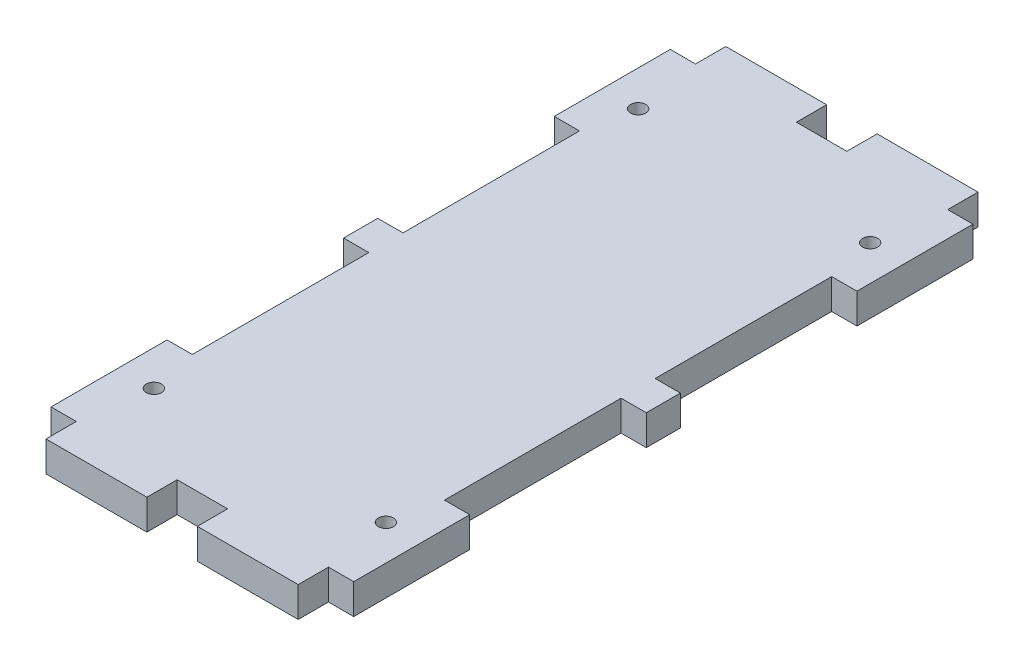
SolidWorks part; units mm, degrees
ref_plane "Plan de face" through (0, 0, 0) normal (0, 0, 1) x (1, 0, 0)
ref_plane "Plan de dessus" through (0, 0, 0) normal (0, 1, 0) x (1, 0, 0)
ref_plane "Plan de droite" through (0, 0, 0) normal (1, 0, 0) x (0, 0, -1)
sketch "Esquisse1" plane through (0, 0, 0) normal (0, 1, 0) x (1, 0, 0)
  line L0 (0, 89.2093) -> (0, -94.1785) construction
  line L1 (-30, 61.38) -> (30, 61.38)
  line L2 (-30, 61.38) -> (-30, -61.38)
  line L3 (-30, -61.38) -> (30, -61.38)
  line L4 (30, 61.38) -> (30, -61.38)
  dimension "D1" = 60
  dimension "D2" = 122.76
  dimension "D3" = 61.38
  dimension "D4" = 30
extrude "Boss.-Extru.1" add sketch "Esquisse1" along normal blind 6
sketch "Esquisse2" plane through (0, 6, 0) normal (0, 1, 0) x (1, 0, 0)
  line L0 (30, 61.38) -> (-30, 61.38) construction
  line L1 (-25, 61.38) -> (-5, 61.38)
  line L2 (-25, 61.38) -> (-25, 67.38)
  line L3 (-25, 67.38) -> (-5, 67.38)
  line L4 (-5, 61.38) -> (-5, 67.38)
  line L6 (5, 61.38) -> (25, 61.38)
  line L7 (5, 61.38) -> (5, 67.38)
  line L8 (5, 67.38) -> (25, 67.38)
  line L9 (25, 61.38) -> (25, 67.38)
  line L10 (-30, 61.38) -> (-30, -61.38) construction
  line L11 (30, -61.38) -> (30, 61.38) construction
  line L12 (-114.0924, 0) -> (165.6917, 0) construction
  line L13 (25, -61.38) -> (25, -67.38)
  line L14 (5, -67.38) -> (25, -67.38)
  line L15 (5, -61.38) -> (5, -67.38)
  line L16 (5, -61.38) -> (25, -61.38)
  line L17 (-5, -61.38) -> (-5, -67.38)
  line L18 (-25, -67.38) -> (-5, -67.38)
  line L19 (-25, -61.38) -> (-25, -67.38)
  line L20 (-25, -61.38) -> (-5, -61.38)
  dimension "D1" = 6
  dimension "D2" = 20
  dimension "D3" = 6
  dimension "D4" = 20
  dimension "D5" = 5
  dimension "D6" = 5
extrude "Boss.-Extru.2" add sketch "Esquisse2" against normal blind 6
sketch "Esquisse3" plane through (0, 6, 0) normal (0, 1, 0) x (1, 0, 0)
  line L0 (73.2715, 0) -> (-73.7315, 0) construction
  line L1 (-60.2107, 48) -> (82.7649, 48) construction
  line L2 (-25, 61.38) -> (-30, 61.38) construction
  line L3 (30, -61.38) -> (30, 61.38) construction
  circle A0 centre (23, 48) radius 1.5
  circle A1 centre (-23, 48) radius 1.5
  circle A2 centre (-23, -48) radius 1.5
  circle A3 centre (23, -48) radius 1.5
  point P5 (-27.5, 61.38)
  dimension "D3" = 3
  dimension "D4" = 3
  dimension "D5" = 46
  dimension "D1" = 13.38
  dimension "D2" = 7
extrude "Enlèv. mat.-Extru.1" cut sketch "Esquisse3" against normal blind 6
sketch "Esquisse4" plane through (0, 6, 0) normal (0, 1, 0) x (1, 0, 0)
  line L0 (-30, 61.38) -> (-30, -61.38) construction
  line L1 (-30, -3.38) -> (-25, -3.38)
  line L2 (-30, -3.38) -> (-30, -38.38)
  line L3 (-30, -38.38) -> (-25, -38.38)
  line L4 (-25, -3.38) -> (-25, -38.38)
  line L5 (0, 78.1772) -> (0, -74.3107) construction
  line L6 (-30, -61.38) -> (-25, -61.38) construction
  line L7 (25, -3.38) -> (25, -38.38)
  line L8 (30, -38.38) -> (25, -38.38)
  line L9 (30, -3.38) -> (30, -38.38)
  line L10 (30, -3.38) -> (25, -3.38)
  line L11 (-25, 61.38) -> (-30, 61.38) construction
  line L12 (-30, 3.38) -> (-25, 3.38)
  line L13 (-30, 3.38) -> (-30, 38.38)
  line L14 (-30, 38.38) -> (-25, 38.38)
  line L15 (-25, 3.38) -> (-25, 38.38)
  line L16 (25, 3.38) -> (25, 38.38)
  line L17 (30, 38.38) -> (25, 38.38)
  line L18 (30, 3.38) -> (30, 38.38)
  line L19 (30, 3.38) -> (25, 3.38)
  point P9 (-27.5, -61.38)
  dimension "D1" = 5
  dimension "D2" = 35
  dimension "D3" = 23
  dimension "D4" = 35
  dimension "D5" = 23
  dimension "D6" = 5
extrude "Enlèv. mat.-Extru.2" cut sketch "Esquisse4" against normal blind 6
equation "\"D3@Esquisse1\"=\"D2@Esquisse1\"/2"
equation "\"D4@Esquisse1\"=\"D1@Esquisse1\"/2"
